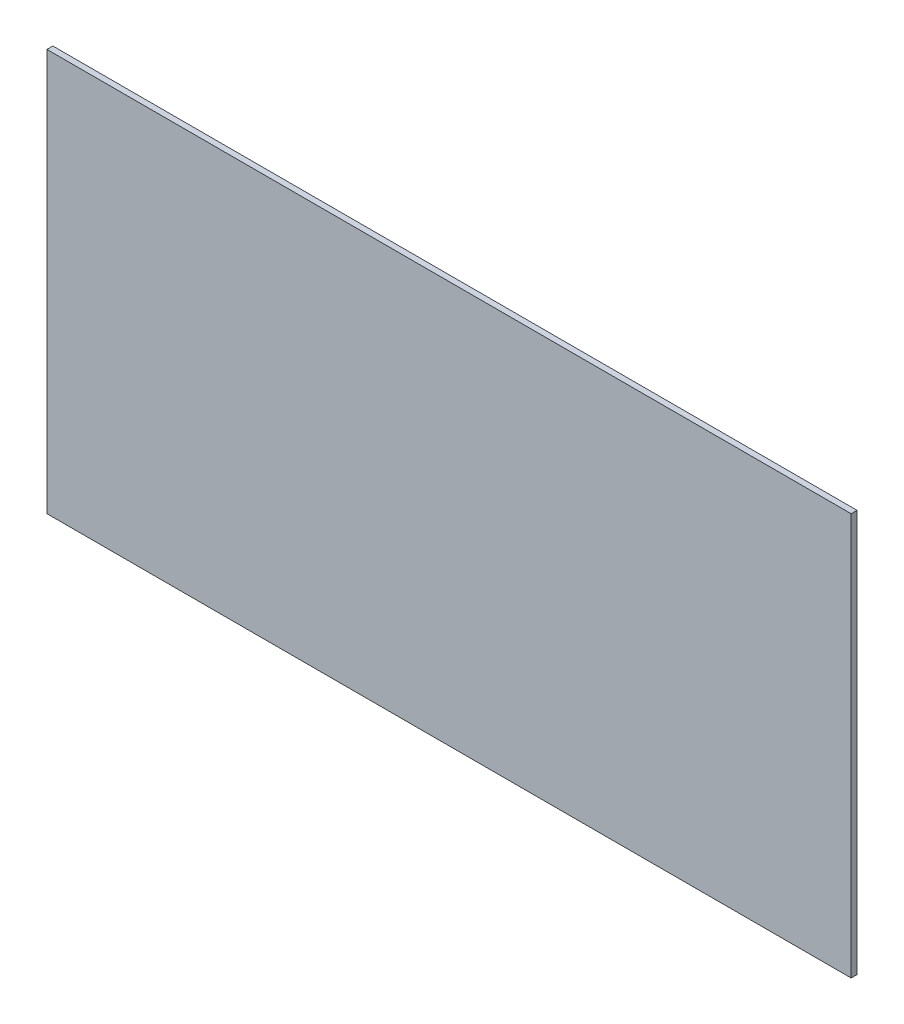
SolidWorks part; units mm, degrees
ref_plane "Front Plane" through (0, 0, 0) normal (0, 0, 1) x (1, 0, 0)
ref_plane "Top Plane" through (0, 0, 0) normal (0, 1, 0) x (1, 0, 0)
ref_plane "Right Plane" through (0, 0, 0) normal (1, 0, 0) x (0, 0, -1)
sketch "Sketch1" plane through (0, 0, 0) normal (0, 0, 1) x (1, 0, 0)
  line L1 (0, 0) -> (863.6, 0)
  line L2 (0, 0) -> (0, 431.8)
  line L3 (0, 431.8) -> (863.6, 431.8)
  line L4 (863.6, 0) -> (863.6, 431.8)
  dimension "D1" = 431.8
  dimension "D2" = 863.6
extrude "Boss-Extrude1" add sketch "Sketch1" along normal blind 6.35
